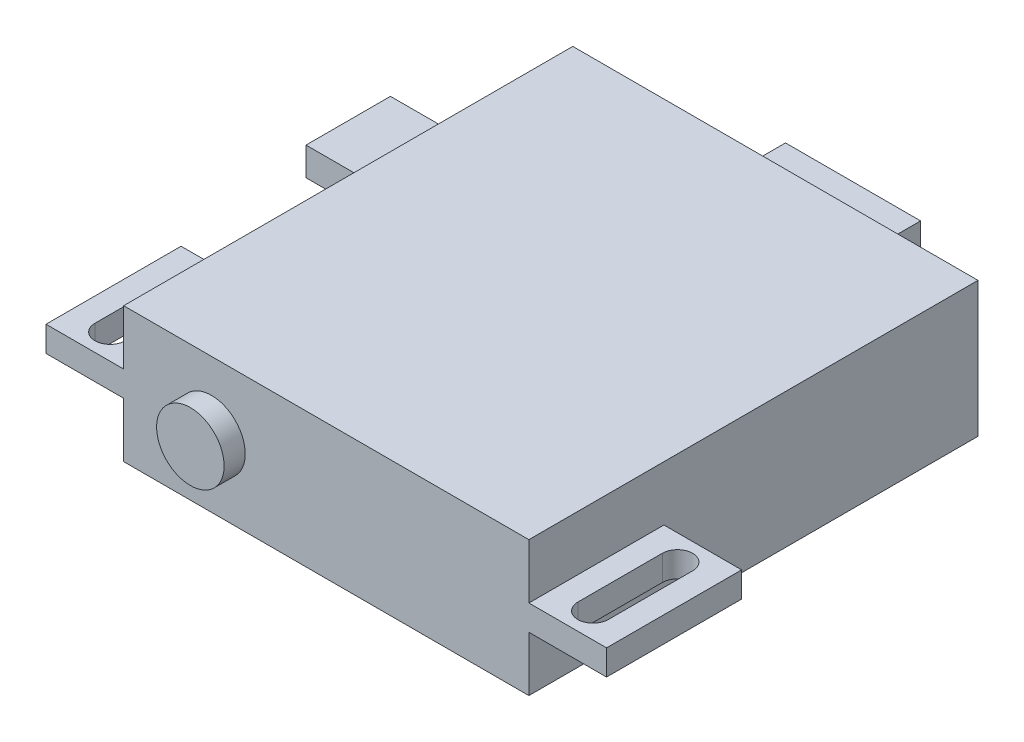
SolidWorks part; units mm, degrees
ref_plane "Front Plane" through (0, 0, 0) normal (0, 0, 1) x (1, 0, 0)
ref_plane "Top Plane" through (0, 0, 0) normal (0, 1, 0) x (1, 0, 0)
ref_plane "Right Plane" through (0, 0, 0) normal (1, 0, 0) x (0, 0, -1)
sketch "Sketch1" plane through (0, 0, 0) normal (0, 1, 0) x (1, 0, 0)
  line L1 (-15.24, 16.891) -> (15.24, 16.891)
  line L2 (-15.24, 16.891) -> (-15.24, -16.891)
  line L3 (-15.24, -16.891) -> (15.24, -16.891)
  line L4 (15.24, 16.891) -> (15.24, -16.891)
  line L5 (-15.24, 16.891) -> (15.24, -16.891) construction
  line L6 (-15.24, -16.891) -> (15.24, 16.891) construction
  point P0 (0, 0)
  dimension "D1" = 30.48
  dimension "D2" = 33.782
extrude "Boss-Extrude1" add sketch "Sketch1" along normal mid plane 10.16
sketch "Sketch2" plane through (0, 0, 16.891) normal (0, 0, 1) x (1, 0, 0)
  line L0 (0, 0) -> (15.24, 0) construction
  line L1 (15.24, 5.08) -> (15.24, -5.08) construction
  line L2 (0, 0) -> (-15.24, 0) construction
  line L3 (-15.24, 5.08) -> (-15.24, -5.08) construction
  circle A0 centre (-8.636, 0) radius 2.54
  point P5 (-8.636, 0)
  dimension "D1" = 5.08
  dimension "D2" = 6.604
extrude "Boss-Extrude2" add sketch "Sketch2" along normal mid plane 3.175
sketch "Sketch3" plane through (0, 0, 0) normal (0, 1, 0) x (1, 0, 0)
  line L0 (15.24, -16.891) -> (15.24, 16.891) construction
  line L1 (15.24, -6.731) -> (21.082, -6.731)
  line L2 (15.24, -6.731) -> (15.24, -16.891)
  line L3 (15.24, -16.891) -> (21.082, -16.891)
  line L4 (21.082, -6.731) -> (21.082, -16.891)
  line L5 (15.24, -6.731) -> (21.082, -16.891) construction
  line L6 (15.24, -16.891) -> (21.082, -6.731) construction
  line L7 (0, 0) -> (0, -16.891) construction
  line L8 (-15.24, -16.891) -> (15.24, -16.891) construction
  line L9 (18.161, -8.636) -> (18.161, -14.986) construction
  line L10 (19.304, -8.636) -> (19.304, -14.986)
  line L11 (17.018, -8.636) -> (17.018, -14.986)
  arc A0 (19.304, -8.636) -> (17.018, -8.636) centre (18.161, -8.636) ccw
  arc A1 (17.018, -14.986) -> (19.304, -14.986) centre (18.161, -14.986) ccw
  point P4 (18.161, -11.811)
  point P15 (18.161, -11.811)
  dimension "D1" = 5.842
  dimension "D2" = 10.16
  dimension "D3" = 2.286
  dimension "D4" = 6.35
extrude "Boss-Extrude3" add sketch "Sketch3" along normal mid plane 1.905
mirror "Mirror1" about plane through (0, 0, 0) normal (1, 0, 0) of "Boss-Extrude3"
sketch "Sketch4" plane through (0, 0, 0) normal (0, 1, 0) x (1, 0, 0)
  line L0 (0, 0) -> (0, 16.891) construction
  line L1 (15.24, 16.891) -> (-15.24, 16.891) construction
  line L2 (-5.08, 16.891) -> (5.08, 16.891)
  line L4 (-5.08, 16.891) -> (-5.08, 22.733)
  line L5 (-5.08, 22.733) -> (5.08, 22.733)
  line L6 (5.08, 16.891) -> (5.08, 22.733)
  line L7 (-3.175, 19.812) -> (3.175, 19.812) construction
  line L8 (-3.175, 20.955) -> (3.175, 20.955)
  line L9 (-5.08, 22.733) -> (5.08, 16.891) construction
  line L10 (5.08, 22.733) -> (-5.08, 16.891) construction
  line L11 (-3.175, 18.669) -> (3.175, 18.669)
  arc A0 (-3.175, 20.955) -> (-3.175, 18.669) centre (-3.175, 19.812) ccw
  arc A1 (3.175, 18.669) -> (3.175, 20.955) centre (3.175, 19.812) ccw
  point P11 (0, 19.812)
  dimension "D1" = 10.16
  dimension "D2" = 5.842
  dimension "D3" = 5.08
  dimension "D4" = 16.891
  dimension "D5" = 2.286
  dimension "D6" = 6.35
extrude "Boss-Extrude4" add sketch "Sketch4" along normal mid plane 1.905
sketch "Sketch5" plane through (-15.24, 0, 0) normal (-1, 0, 0) x (0, 0, 1)
  line L0 (-7.62, 0) -> (0, 0) construction
  line L1 (-10.795, 1.0656) -> (-4.445, 1.0656)
  line L2 (-10.795, 1.0656) -> (-10.795, -1.0656)
  line L3 (-10.795, -1.0656) -> (-4.445, -1.0656)
  line L4 (-4.445, 1.0656) -> (-4.445, -1.0656)
  line L5 (-10.795, 1.0656) -> (-4.445, -1.0656) construction
  line L6 (-10.795, -1.0656) -> (-4.445, 1.0656) construction
  point P0 (-7.62, 0)
  dimension "D1" = 6.35
  dimension "D2" = 7.62
extrude "Boss-Extrude5" add sketch "Sketch5" along normal blind 7.62
